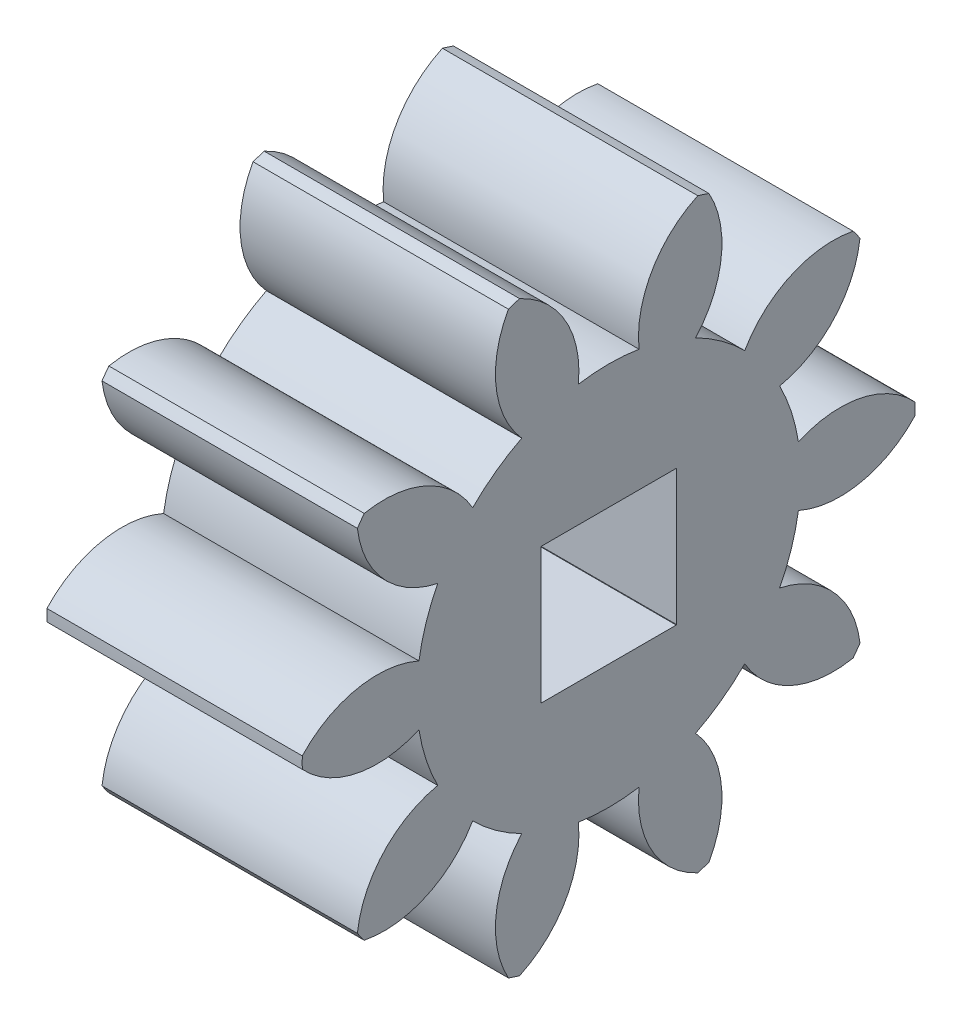
SolidWorks part; units mm, degrees
ref_plane "Plane1" through (0, 0, 0) normal (0, 0, 1) x (1, 0, 0)
ref_plane "Plane2" through (0, 0, 0) normal (0, 1, 0) x (1, 0, 0)
ref_plane "Plane3" through (0, 0, 0) normal (1, 0, 0) x (0, 0, -1)
sketch "HoldingSke" plane through (0, 0, 0) normal (0, 1, 0) x (1, 0, 0)
  line L0 (0, 0) -> (500.2823, -88.2133)
  line L1 (-15, 0) -> (100, 0) construction
  line L2 (0, 0) -> (-2.1039, 2.3779)
  line L3 (0, 0) -> (-11.863, 4.5341)
  line L4 (0, 0) -> (8.5048, 1.4996)
  line L5 (0, 0) -> (-47.5972, -17.7524)
  line L6 (0, 0) -> (-5.2639, -3.5516)
  line L7 (-2.1039, 2.3779) -> (8.8308, 51.9871)
  line L8 (-76.2, 54.61) -> (-71.1708, 54.61)
  line L9 (-71.009, 38.7566) -> (-53.1078, 45.2721)
  line L10 (-76.2, 71.12) -> (104.1128, 71.12)
  line L11 (0, 0) -> (-6.35, 0)
  line L12 (-76.2, 101.6) -> (-76.1492, 101.6)
  line L13 (24.9733, 27.94) -> (52.9518, 28.4284)
  line L14 (24.9733, 27.94) -> (25.0241, 27.9398)
  line L15 (24.9733, 27.94) -> (100.4021, 29.52)
  circle A0 centre (0, 0) radius 2.3813
  circle A1 centre (0, 0) radius 4.7752
  circle A2 centre (0, 0) radius 38.1
  circle A3 centre (0, 0) radius 2.3813
  dimension "MHD" = 9.5504
  dimension "Hub_dia" = 76.2
  dimension "Bore" = 4.7625
  dimension "MBD" = 4.7625
  dimension "Num_teeth" = 10
  dimension "Pitch" = 508
  dimension "Overall_len" = 50.8
  dimension "Show_teeth" = 10
  dimension "Thickness" = 6.35
  dimension "OAL" = 50.8001
  dimension "T_dim" = 5.0292
  dimension "Ap" = 20
  dimension "H" = 19.05
  dimension "Pitch_radius" = 180.3128
  dimension "Width" = 6.35
  dimension "Backlash" = 0.0508
  dimension "Addendum_fac" = 1
  dimension "Dedendum_fac" = 1.2
  dimension "Clearance_fac" = 0.2
  dimension "Dedendum_add" = 0.0508
sketch "BasProSke" plane through (0, 0, 0) normal (0, 1, 0) x (1, 0, 0)
  line L0 (-10, 0) -> (60, 0) construction
  line L1 (0, 0) -> (0, 7.62)
  line L2 (0, 0) -> (6.35, 0)
  line L3 (6.35, 0) -> (6.35, 7.62)
  line L4 (6.35, 7.62) -> (0, 7.62)
  dimension "Thickness" = 6.35
  dimension "Diameter" = 15.24
revolve "Base-Revolve" add sketch "BasProSke" angle 360 about L0
sketch "TooCutSke" plane through (0, 0, 0) normal (1, 0, 0) x (0, 0, -1)
  line L1 (0, 0) -> (0, 107) construction
  line L2 (0, 0) -> (-1.0821, 6.2571) construction
  line L3 (0, 0) -> (-3.8845, 11.9553) construction
  line L4 (-1.0821, 6.2571) -> (-1.9423, 5.9776) construction
  arc A0 (0.7546, 4.7152) -> (-0.7546, 4.7152) centre (0, 0) ccw
  arc A1 (2.2508, 7.3066) -> (-2.2508, 7.3066) centre (0, 0) ccw
  circle A2 centre (0, 0) radius 6.35 construction
  circle A3 centre (0, 0) radius 5.967 construction
  arc A4 (-0.7546, 4.7152) -> (-2.2508, 7.3066) centre (-3.2803, 4.9845) ccw
  arc A5 (2.2508, 7.3066) -> (0.7546, 4.7152) centre (3.2803, 4.9845) ccw
  dimension "Root_dia" = 9.5504
  dimension "Overcut_dia" = 15.2908
  dimension "Pitch_dia" = 12.7
  dimension "Base_dia" = 11.9341
  dimension "Flank_rad" = 2.54
  dimension "Half_ang" = 18
  dimension "Half_CT" = 0.9045
extrude "ToothCut" cut sketch "TooCutSke" along normal through all
fillet "Breaks" [suppressed] radius 0.0254
fillet "RootFillets" [suppressed] radius 0.3048
pattern_circular "TeethCuts" count 10 every 36 about axis through (-10, 0, 0) along (1, 0, 0) of "ToothCut", "RootFillets", "Breaks"
sketch "HubNeaOneSke" plane through (0, 0, 0) normal (-1, 0, 0) x (0, 0, 1)
  circle A0 centre (0, 0) radius 4.7752
  dimension "Diameter" = 9.5504
extrude "HubNearOne" [suppressed] add sketch "HubNeaOneSke" along normal blind 44.4501
sketch "HubNeaBotSke" plane through (0, 0, 0) normal (-1, 0, 0) x (0, 0, 1)
  circle A0 centre (0, 0) radius 4.7752
  dimension "Diameter" = 9.5504
extrude "HubNearBoth" [suppressed] add sketch "HubNeaBotSke" along normal blind 22.225
ref_plane "FarPln" through (6.35, 0, 0) normal (1, 0, 0) x (0, 0, -1)
sketch "HubFarSke" plane through (6.35, 0, 0) normal (1, 0, 0) x (0, 0, -1)
  circle A0 centre (0, 0) radius 4.7752
  dimension "Diameter" = 9.5504
extrude "HubFar" [suppressed] add sketch "HubFarSke" along normal blind 22.225
sketch "BorSke" plane through (0, 0, 0) normal (1, 0, 0) x (0, 0, -1)
  circle A0 centre (0, 0) radius 2.3813
  dimension "Diameter" = 4.7625
extrude "Bore" cut sketch "BorSke" along normal mid plane 101.6001
sketch "KeySke" plane through (0, 0, 0) normal (1, 0, 0) x (0, 0, -1)
  line L0 (-0.127, 0) -> (-0.127, 2.648)
  line L1 (-0.127, 2.648) -> (0.127, 2.648)
  line L2 (0.127, 2.648) -> (0.127, 0)
  line L3 (0, 0) -> (0, 34) construction
  line L4 (-0.127, 0) -> (0.127, 0)
  dimension "Offset" = 2.648
  dimension "Width" = 0.254
extrude "Keyway" [suppressed] cut sketch "KeySke" along normal mid plane 101.6001
pattern_circular "Keyway2" [suppressed] count 2 every 90 about axis through (-10, 0, 0) along (1, 0, 0)
sketch "Sketch1" plane through (6.35, 0, 0) normal (1, 0, 0) x (0, 0, -1)
  line L1 (1.6875, -1.6875) -> (-1.6875, -1.6875)
  line L2 (1.6875, -1.6875) -> (1.6875, 1.6875)
  line L3 (1.6875, 1.6875) -> (-1.6875, 1.6875)
  line L4 (-1.6875, -1.6875) -> (-1.6875, 1.6875)
  line L5 (1.6875, -1.6875) -> (-1.6875, 1.6875) construction
  line L6 (1.6875, 1.6875) -> (-1.6875, -1.6875) construction
  circle A0 centre (0, 0) radius 2.3813
  circle M3 centre (0, 0) radius 2.3813
  dimension "D1" = 3.375
  dimension "D2" = 3.375
extrude "Boss-Extrude1" add sketch "Sketch1" against normal up to surface (6.35 mm away) contours L3 M3 | L4 M3 | L1 M3 | L2 M3 up to face at (0, 0, -2.3813)
equation "' \"Pitch@HoldingSke\" = 4"
equation "' \"Num_teeth@HoldingSke\" = 12"
equation "' \"Ap@HoldingSke\" =  20"
equation "' \"Ap@HoldingSke\" = 20"
equation "' \"Width@HoldingSke\" = 0.5"
equation "' \"Hub_dia@HoldingSke\"= 1"
equation "' \"Hub_dia@HoldingSke\" = 1"
equation "' \"Overall_len@HoldingSke\" = 1.0"
equation "' \"Bore@HoldingSke\" = 0.75"
equation "' \"T_dim@HoldingSke\" = 0.85"
equation "' \"Width@KeySke\" = 0.25"
equation "' \"Show_teeth@HoldingSke\" = 13"
equation "' \"Backlash@HoldingSke\" = 0.009"
equation "' \"Addendum_fac@HoldingSke\" = 1.0"
equation "' \"Dedendum_fac@HoldingSke\" = 1.25"
equation "' \"Dedendum_add@HoldingSke\" = 0.00005"
equation "' \"Clearance_fac@HoldingSke\" = 0.25"
equation "' \"Pitch@HoldingSke\" = 0.5"
equation "' \"Num_teeth@HoldingSke\" = 23"
equation "' \"Show_teeth@HoldingSke\" = 23"
equation "' \"Backlash@HoldingSke\" = 0.0375"
equation "\"Overcut_dia@TooCutSke\" = (\"Num_teeth@HoldingSke\" + 2 * \"Addendum_fac@HoldingSke\") / \"Pitch@HoldingSke\" + 0.002"
equation "\"Pitch_dia@TooCutSke\" = \"Num_teeth@HoldingSke\" / \"Pitch@HoldingSke\""
equation "\"Base_dia@TooCutSke\" = \"Num_teeth@HoldingSke\" / \"Pitch@HoldingSke\" * cos((\"Ap@HoldingSke\"  * 3.14159265 / 180))"
equation "\"Root_dia@TooCutSke\" = (\"Num_teeth@HoldingSke\" + 2) / \"Pitch@HoldingSke\" - 2 * (\"Addendum_fac@HoldingSke\" + \"Dedendum_fac@HoldingSke\") / \"Pitch@HoldingSke\" - \"Dedendum_add@HoldingSke\" * 2"
equation "\"Half_ang@TooCutSke\" = 180 / \"Num_teeth@HoldingSke\""
equation "\"Half_CT@TooCutSke\" = \"Num_teeth@HoldingSke\" / \"Pitch@HoldingSke\" * sin((3.14159265 / 2 / \"Num_teeth@HoldingSke\")) / 2 - 7 * \"Backlash@HoldingSke\" / 4"
equation "\"Flank_rad@TooCutSke\" = \"Num_teeth@HoldingSke\" / \"Pitch@HoldingSke\" / 5"
equation "\"Radius@RootFillets\" = \"Clearance_fac@HoldingSke\" / \"Pitch@HoldingSke\" + \"Dedendum_add@HoldingSke\""
equation "\"Break_rad@Breaks\" = 0.02 / \"Pitch@HoldingSke\""
equation "\"Thickness@HoldingSke\" = \"Width@HoldingSke\""
equation "\"OAL@HoldingSke\" = \"Thickness@HoldingSke\""
equation "\"MHD@HoldingSke\" = (\"Num_teeth@HoldingSke\" + 2) / \"Pitch@HoldingSke\" - 2 * (\"Addendum_fac@HoldingSke\" + \"Dedendum_fac@HoldingSke\")  / \"Pitch@HoldingSke\" - \"Dedendum_add@HoldingSke\" * 2"
equation "\"MBD@HoldingSke\" = (\"Num_teeth@HoldingSke\" + 2) / \"Pitch@HoldingSke\" - 2 * (\"Addendum_fac@HoldingSke\" + \"Dedendum_fac@HoldingSke\")  / \"Pitch@HoldingSke\" - \"Dedendum_add@HoldingSke\" * 2 - 0.002"
equation "\"MHD@HoldingSke\" = ((sgn( \"MHD@HoldingSke\" - \"Hub_dia@HoldingSke\" )-1)*( \"MHD@HoldingSke\" - \"Hub_dia@HoldingSke\" ))/-2+ \"Hub_dia@HoldingSke\""
equation "\"MBD@HoldingSke\" = ((sgn( \"MBD@HoldingSke\" - \"Bore@HoldingSke\" )-1)*( \"MBD@HoldingSke\" - \"Bore@HoldingSke\" ))/-2+ \"Bore@HoldingSke\""
equation "\"OAL@HoldingSke\" = ((sgn( \"OAL@HoldingSke\" - \"Overall_len@HoldingSke\" )+1)*( \"OAL@HoldingSke\" - \"Overall_len@HoldingSke\" ))/2 + \"Overall_len@HoldingSke\" + 0.000002"
equation "\"Num_teeth@TeethCuts\" = int( \"Show_teeth@HoldingSke\" ) + 1"
equation "\"Num_teeth@TeethCuts\" = ((sgn( \"Num_teeth@TeethCuts\" - \"Num_teeth@HoldingSke\" )-1)*( \"Num_teeth@TeethCuts\" - \"Num_teeth@HoldingSke\" ))/-2+ \"Num_teeth@HoldingSke\""
equation "\"Num_teeth@TeethCuts\" = ((sgn( \"Num_teeth@TeethCuts\" - 2.0)+1)*( \"Num_teeth@TeethCuts\" - 2.0))/2 +2.0"
equation "\"Angle@TeethCuts\" = 360.0 / \"Num_teeth@HoldingSke\""
equation "\"Diameter@BasProSke\" = (\"Num_teeth@HoldingSke\" + 2 * \"Addendum_fac@HoldingSke\") / \"Pitch@HoldingSke\""
equation "\"Thickness@BasProSke\"  = \"Thickness@HoldingSke\""
equation "' \"Fillet_rad@BasProSke\" =  \"Thickness@HoldingSke\" * 0.05"
equation "' \"Fillet_rad@BasProSke\" = \"Thickness@HoldingSke\" * 0.05"
equation "\"MHD@HoldingSke\" = ((sgn( \"MHD@HoldingSke\" - \"Root_dia@TooCutSke\" )-1)*( \"MHD@HoldingSke\" - \"Root_dia@TooCutSke\" ))/-2+ \"Root_dia@TooCutSke\""
equation "\"Diameter@HubNeaOneSke\" = \"MHD@HoldingSke\""
equation "\"Length@HubNearOne\" = \"OAL@HoldingSke\" - \"Thickness@BasProSke\""
equation "\"Diameter@HubNeaBotSke\" = \"MHD@HoldingSke\""
equation "\"Length@HubNearBoth\" = ( \"OAL@HoldingSke\" - \"Thickness@BasProSke\" ) / 2.0"
equation "\"Thickness@FarPln\" = \"Thickness@BasProSke\""
equation "\"Diameter@HubFarSke\" = \"MHD@HoldingSke\""
equation "\"Length@HubFar\" = ( \"OAL@HoldingSke\" - \"Thickness@BasProSke\" ) / 2.0"
equation "\"Diameter@BorSke\" = \"MBD@HoldingSke\""
equation "\"D1@Bore\" = \"OAL@HoldingSke\" * 2.0"
equation "\"D1@Keyway\" = \"OAL@HoldingSke\" * 2.0"
equation "\"Offset@KeySke\" = \"T_dim@HoldingSke\" - \"MBD@HoldingSke\" / 2.0"
